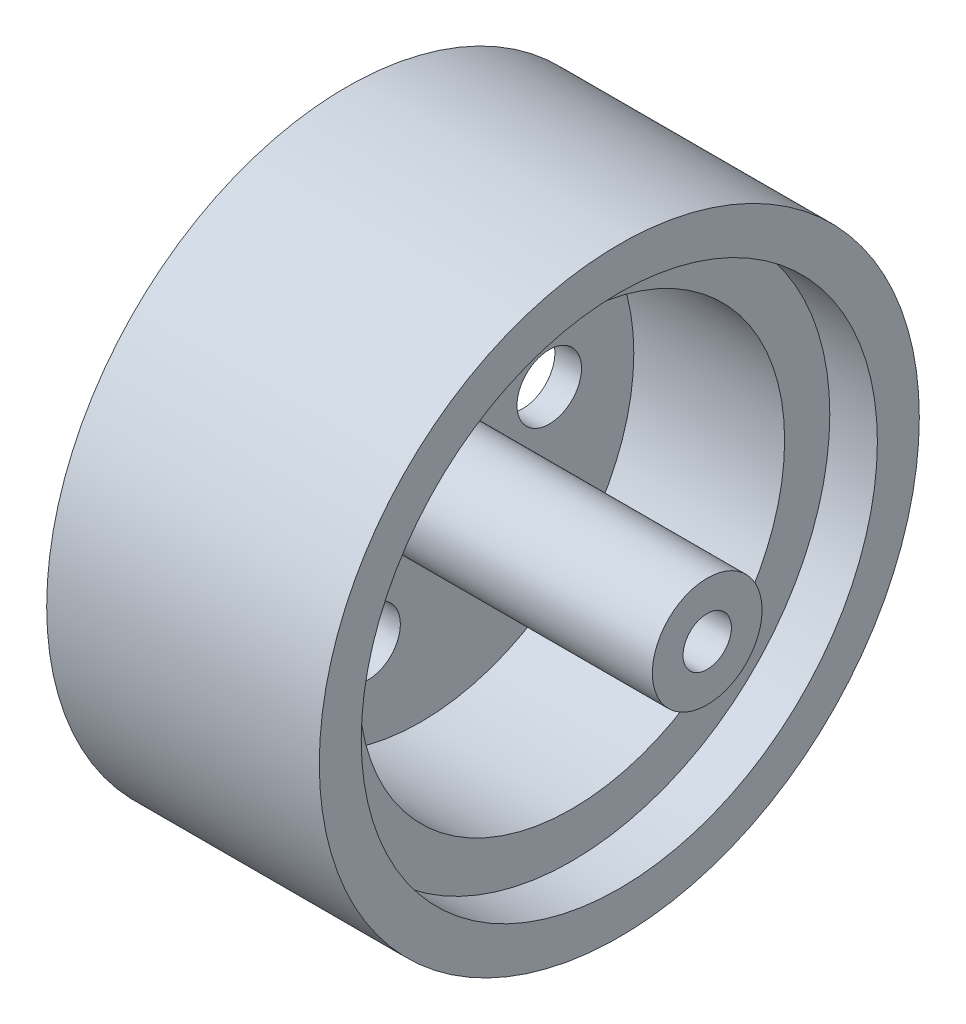
SolidWorks part; units mm, degrees
ref_plane "正面" through (0, 0, 0) normal (0, 0, 1) x (1, 0, 0)
ref_plane "平面" through (0, 0, 0) normal (0, 1, 0) x (1, 0, 0)
ref_plane "右側面" through (0, 0, 0) normal (1, 0, 0) x (0, 0, -1)
sketch "ｽｹｯﾁ1" plane through (0, 0, 0) normal (1, 0, 0) x (0, 0, -1)
  circle A0 centre (0, 0) radius 16
  dimension "D1" = 32
extrude "ﾎﾞｽ - 押し出し1" add sketch "ｽｹｯﾁ1" along normal blind 11 contours A0
sketch "ｽｹｯﾁ2" plane through (11, 0, 0) normal (1, 0, 0) x (0, 0, -1)
  circle A0 centre (0, 0) radius 13.2
  circle A1 centre (0, 0) radius 16 construction
  dimension "D1" = 2.8
extrude "ｶｯﾄ - 押し出し1" cut sketch "ｽｹｯﾁ2" against normal blind 9.35
sketch "ｽｹｯﾁ3" plane through (0, 0, 0) normal (-1, 0, 0) x (0, 0, 1)
  circle A0 centre (4.6857, 6.4842) radius 2
  dimension "D2" = 4
  dimension "D1" = 8
extrude "ｶｯﾄ - 押し出し3" cut sketch "ｽｹｯﾁ3" against normal blind 9.35
pattern_circular "円形ﾊﾟﾀｰﾝ3" count 3 over 360 about axis through (0, 0, 0) along (1, 0, 0) of "ｶｯﾄ - 押し出し3"
sketch "ｽｹｯﾁ4" plane through (1.65, 0, 0) normal (1, 0, 0) x (0, 0, -1)
  circle A0 centre (0, 0) radius 3.4
  dimension "D1" = 6.8
extrude "ﾎﾞｽ - 押し出し2" add sketch "ｽｹｯﾁ4" along normal blind 17.75
sketch "ｽｹｯﾁ5" plane through (19.4, 0, 0) normal (1, 0, 0) x (0, 0, -1)
  circle A0 centre (0, 0) radius 1.5
  dimension "D1" = 3
extrude "ｶｯﾄ - 押し出し4" cut sketch "ｽｹｯﾁ5" against normal blind 25.75
sketch "ｽｹｯﾁ6" plane through (0, 0, 0) normal (-1, 0, 0) x (0, 0, 1)
  circle A0 centre (0, 0) radius 18.6
  circle A1 centre (0, 0) radius 16
  dimension "D1" = 37.2
extrude "ﾎﾞｽ - 押し出し4" add sketch "ｽｹｯﾁ6" against normal blind 13.95 and the other way blind 2.95
